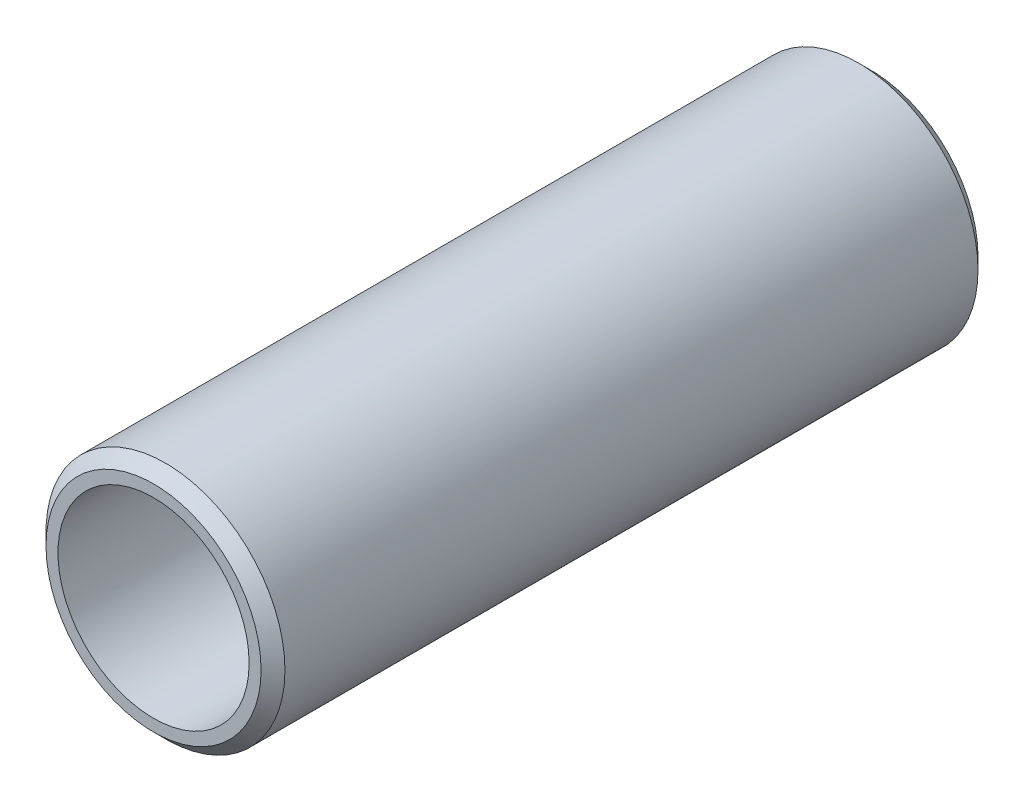
SolidWorks part; units mm, degrees
material "Brass"
ref_plane "Front Plane" through (0, 0, 0) normal (0, 0, 1) x (1, 0, 0)
ref_plane "Top Plane" through (0, 0, 0) normal (0, 1, 0) x (1, 0, 0)
ref_plane "Right Plane" through (0, 0, 0) normal (1, 0, 0) x (0, 0, -1)
sketch "Sketch1" plane through (0, 0, 0) normal (0, 0, 1) x (1, 0, 0)
  circle A0 centre (0, 0) radius 4
  dimension "D1" = 8
extrude "Extrude-Thin1" add sketch "Sketch1" along normal blind 30 thin
chamfer "Chamfer1" distance 0.5 angle 45 2 edges at (5, 0, 0) (5, 0, 30)
